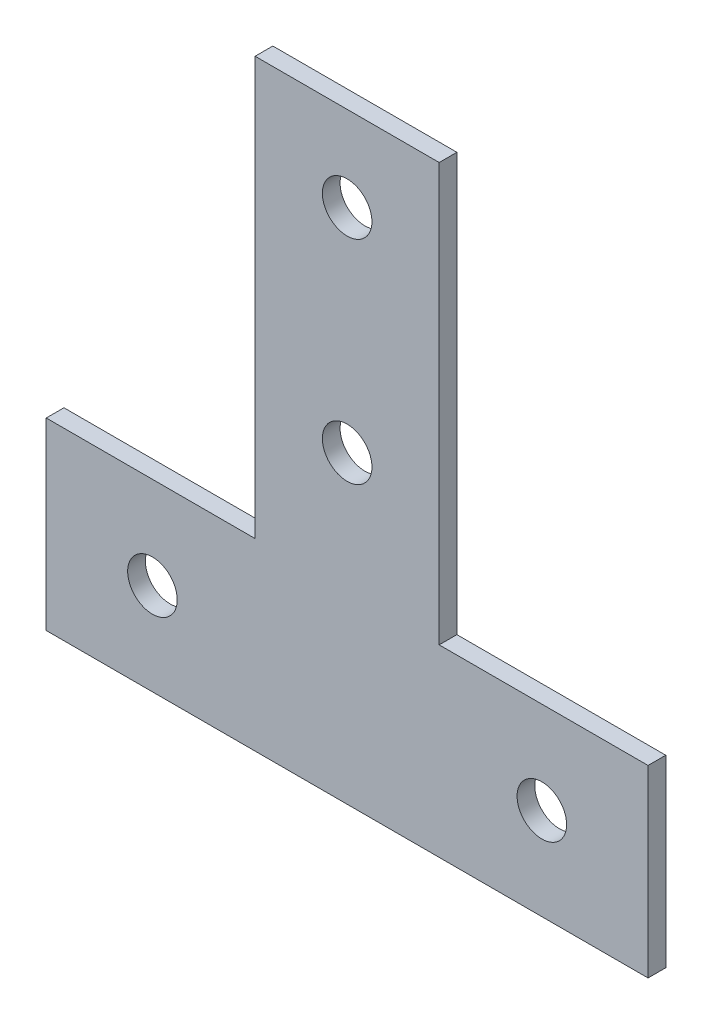
SolidWorks part; units mm, degrees
ref_plane "Спереди" through (0, 0, 0) normal (0, 0, 1) x (1, 0, 0)
ref_plane "Сверху" through (0, 0, 0) normal (0, 1, 0) x (1, 0, 0)
ref_plane "Справа" through (0, 0, 0) normal (1, 0, 0) x (0, 0, -1)
sketch "Эскиз1" plane through (0, 0, 0) normal (0, 0, 1) x (1, 0, 0)
  line L0 (-42.5, 0) -> (42.5, 0)
  line L1 (-42.5, 0) -> (-42.5, 26)
  line L2 (-42.5, 26) -> (-13, 26)
  line L3 (-13, 26) -> (-13, 85)
  line L4 (-13, 85) -> (13, 85)
  line L5 (13, 85) -> (13, 26)
  line L6 (13, 26) -> (42.5, 26)
  line L7 (42.5, 26) -> (42.5, 0)
  line L8 (-27.5, 13) -> (27.5, 13) construction
  circle A0 centre (0, 73) radius 3.5
  circle A1 centre (0, 43) radius 3.5
  circle A2 centre (-27.5, 13) radius 3.5
  circle A3 centre (27.5, 13) radius 3.5
  point P4 (0, 0)
  point P18 (0, 13)
  point P19 (42.5, 13)
  dimension "D5" = 12
  dimension "D6" = 30
  dimension "D7" = 7
  dimension "D1" = 85
  dimension "D2" = 85
  dimension "D3" = 26
  dimension "D4" = 55
extrude "Бобышка-Вытянуть1" add sketch "Эскиз1" along normal blind 2.5
